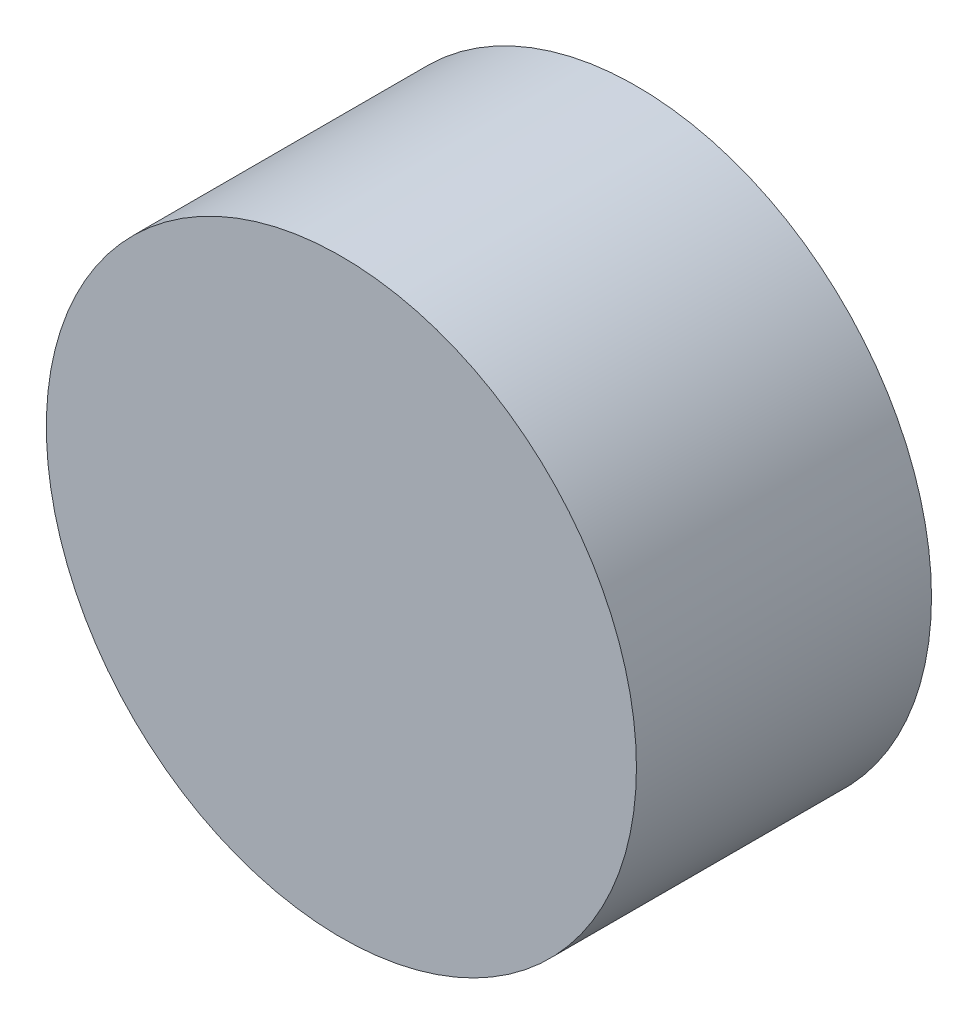
SolidWorks part; units mm, degrees
ref_plane "Front Plane" through (0, 0, 0) normal (0, 0, 1) x (1, 0, 0)
ref_plane "Top Plane" through (0, 0, 0) normal (0, 1, 0) x (1, 0, 0)
ref_plane "Right Plane" through (0, 0, 0) normal (1, 0, 0) x (0, 0, -1)
sketch "Sketch1" plane through (0, 0, 0) normal (0, 0, 1) x (1, 0, 0)
  circle A0 centre (0, 0) radius 2
  dimension "D1" = 4
extrude "Boss-Extrude1" add sketch "Sketch1" along normal mid plane 2
